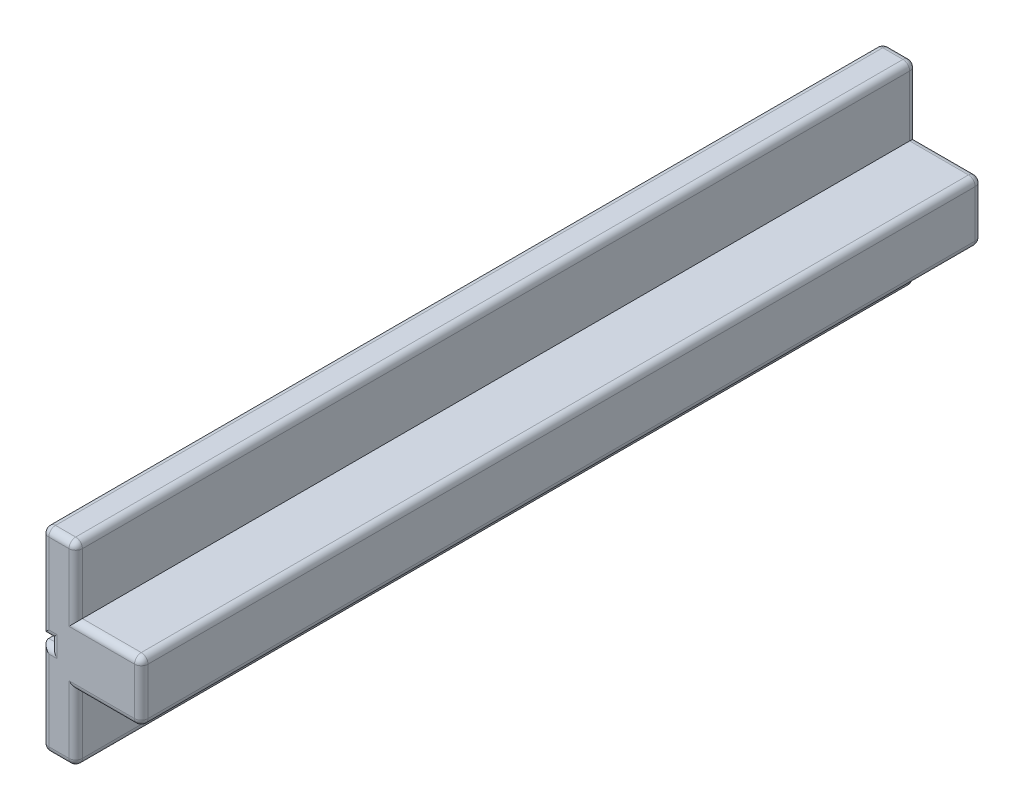
SolidWorks part; units mm, degrees
ref_plane "Ebene vorne" through (0, 0, 0) normal (0, 0, 1) x (1, 0, 0)
ref_plane "Ebene oben" through (0, 0, 0) normal (0, 1, 0) x (1, 0, 0)
ref_plane "Ebene rechts" through (0, 0, 0) normal (1, 0, 0) x (0, 0, -1)
sketch "Skizze1" plane through (0, 0, 0) normal (0, 0, 1) x (1, 0, 0)
  line L1 (2.95, 2) -> (1, 2)
  line L2 (2.95, 2) -> (2.95, 3.8)
  line L3 (2.95, 3.8) -> (1, 3.8)
  line L5 (0, 3.01) -> (0.25, 3.01)
  line L6 (0.25, 3.01) -> (0.25, 2.79)
  line L11 (0.25, 2.79) -> (0, 2.79)
  line L12 (0, 3.01) -> (0, 5.8)
  line L13 (1, 0) -> (0, 0)
  line L14 (1, 0) -> (1, 2)
  line L15 (1, 5.8) -> (0, 5.8)
  line L16 (0, 0) -> (0, 2.79)
  line L24 (1, 3.8) -> (1, 5.8)
  dimension "D1" = 1.8
  dimension "D2" = 5.8
  dimension "D3" = 1
  dimension "D4" = 2.95
  dimension "D5" = 0.22
  dimension "D6" = 0.25
extrude "Aufsatz-Linear austragen1" add sketch "Skizze1" along normal blind 25
fillet "Verrundung1" radius 0.2 30 edges at (0.125, 3.01, 0) (0.25, 2.9, 0) (0.125, 2.79, 0) (0, 1.395, 0) (1, 1, 0) (1.975, 2, 0) (1.975, 3.8, 0) (1, 4.8, 0) (0, 4.405, 0) (0, 0, 12.5) (1, 0, 12.5) (0.5, 0, 0) (1, 4.8, 25) (1.975, 3.8, 25) (1.975, 2, 25) (1, 1, 25) (0.5, 0, 25) (0, 1.395, 25) (0.125, 2.79, 25) (0.25, 2.9, 25) (0.125, 3.01, 25) (0, 4.405, 25) (2.95, 2, 12.5) (2.95, 2.9, 25) (2.95, 3.8, 12.5) (2.95, 2.9, 0) (1, 5.8, 12.5) (0.5, 5.8, 25) (0, 5.8, 12.5) (0.5, 5.8, 0)
